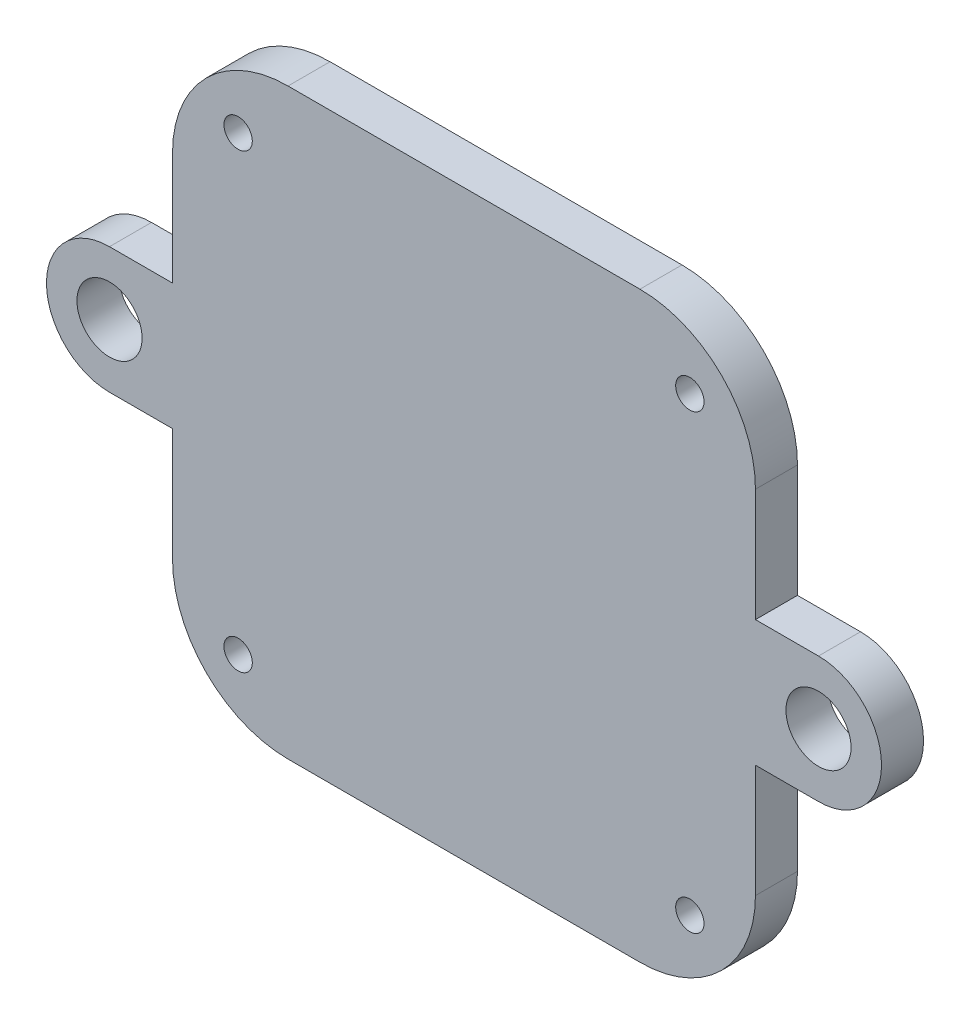
SolidWorks part; units mm, degrees
ref_plane "Front Plane" through (0, 0, 0) normal (0, 0, 1) x (1, 0, 0)
ref_plane "Top Plane" through (0, 0, 0) normal (0, 1, 0) x (1, 0, 0)
ref_plane "Right Plane" through (0, 0, 0) normal (1, 0, 0) x (0, 0, -1)
sketch "Sketch1" plane through (0, 0, 0) normal (0, 0, 1) x (1, 0, 0)
  line L0 (16.75, -27.7449) -> (-16.75, -27.7449) construction
  line L1 (-27.7449, 16.75) -> (-27.7449, -16.75) construction
  line L2 (16.75, 27.7449) -> (-16.75, 27.7449) construction
  line L3 (27.7449, -16.75) -> (27.7449, 16.75) construction
  line L4 (16.75, -27.7449) -> (-16.75, -27.7449)
  line L5 (-27.7449, 16.75) -> (-27.7449, -16.75)
  line L6 (16.75, 27.7449) -> (-16.75, 27.7449)
  line L7 (27.7449, -16.75) -> (27.7449, 16.75)
  line L8 (16.75, 27.7449) -> (-16.75, -27.7449) construction
  line L9 (-39.7449, 0) -> (39.7449, 0) construction
  line L10 (39.7449, 6) -> (-39.7449, 6)
  line L11 (39.7449, 6) -> (39.7449, -6)
  line L12 (39.7449, -6) -> (-39.7449, -6)
  line L13 (-39.7449, 6) -> (-39.7449, -6)
  line L14 (39.7449, 6) -> (-39.7449, -6) construction
  line L15 (39.7449, -6) -> (-39.7449, 6) construction
  line L16 (0, 27.7449) -> (0, -27.7449) construction
  arc A0 (16.75, -27.7449) -> (27.7449, -16.75) centre (16.75, -16.75) ccw construction
  arc A1 (-27.7449, -16.75) -> (-16.75, -27.7449) centre (-16.75, -16.75) ccw construction
  arc A2 (-16.75, 27.7449) -> (-27.7449, 16.75) centre (-16.75, 16.75) ccw construction
  arc A3 (27.7449, 16.75) -> (16.75, 27.7449) centre (16.75, 16.75) ccw construction
  arc A4 (-27.7449, -16.75) -> (-16.75, -27.7449) centre (-16.75, -16.75) ccw
  arc A5 (-16.75, 27.7449) -> (-27.7449, 16.75) centre (-16.75, 16.75) ccw
  arc A6 (27.7449, 16.75) -> (16.75, 27.7449) centre (16.75, 16.75) ccw
  arc A7 (16.75, -27.7449) -> (27.7449, -16.75) centre (16.75, -16.75) ccw
  circle A8 centre (21.5, 21.5) radius 1.35
  arc A10 (21.5, 20.4935) -> (21.5, 22.5065) centre (21.5, 21.5) ccw construction
  circle A11 centre (-21.5, 21.5) radius 1.35
  arc A12 (-21.5, 22.5065) -> (-21.5, 20.4935) centre (-21.5, 21.5) ccw construction
  circle A13 centre (-21.5, -21.5) radius 1.35
  arc A14 (-21.5, -20.4935) -> (-21.5, -22.5065) centre (-21.5, -21.5) ccw construction
  circle A15 centre (21.5, -21.5) radius 1.35
  arc A16 (21.5, -20.4935) -> (21.5, -22.5065) centre (21.5, -21.5) ccw construction
  circle A17 centre (-33.7449, 0) radius 3.1
  circle A18 centre (-33.7449, 0) radius 6
  circle A19 centre (33.7449, 0) radius 3.1
  circle A20 centre (33.7449, 0) radius 6
  point P32 (0, 0)
  dimension "D1" = 2.7
  dimension "D2" = 6.2
  dimension "D3" = 12
extrude "Boss-Extrude1" add sketch "Sketch1" against normal blind 4 contours L7 A6 L6 A5 L5 L10 A11 A8 | L12 L7 L10 L5 | L4 A7 L7 L12 L5 A4 A15 A13 | A18 L12 L5 | A18 L5 L10 | A18 A17 | L7 A20 L10 | L12 A20 L7 | A20 A19
hole_wizard "CSK for M2.5 Flat Head Machine Screw1" positions "Sketch2" profile "Sketch3" countersink size "M2.5" standard "ANSI Metric" end condition through all
sketch "Sketch2" plane through (0, 0, -4) normal (0, 0, -1) x (-1, 0, 0)
  point P0 (-21.5, 21.5)
  point P3 (21.5, 21.5)
  point P6 (21.5, -21.5)
  point P9 (-21.5, -21.5)
sketch "Sketch3" plane through (21.5, 21.5, -4) normal (1, 0, 0) x (0, 1, 0)
  line L0 (0, 0) -> (0, 4)
  line L1 (0, 4) -> (1.25, 4)
  line L2 (1.25, 4) -> (1.25, 1.55)
  line L3 (1.25, 1.55) -> (2.5, 0.3)
  line L4 (2.5, 0.3) -> (2.5, 0)
  line L6 (2.5, 0) -> (0, 0)
  line L7 (-1.25, 1.55) -> (-2.5, 0.3) construction
  line L11 (0, -6.35) -> (0, 107.95) construction
  dimension "Thru Hole Dia." = 2.5
  dimension "Thru Hole Depth" = 4
  dimension "C'Sink Dia." = 5
  dimension "C'Sink Angle" = 90
  dimension "Head Clearance" = 0.3
